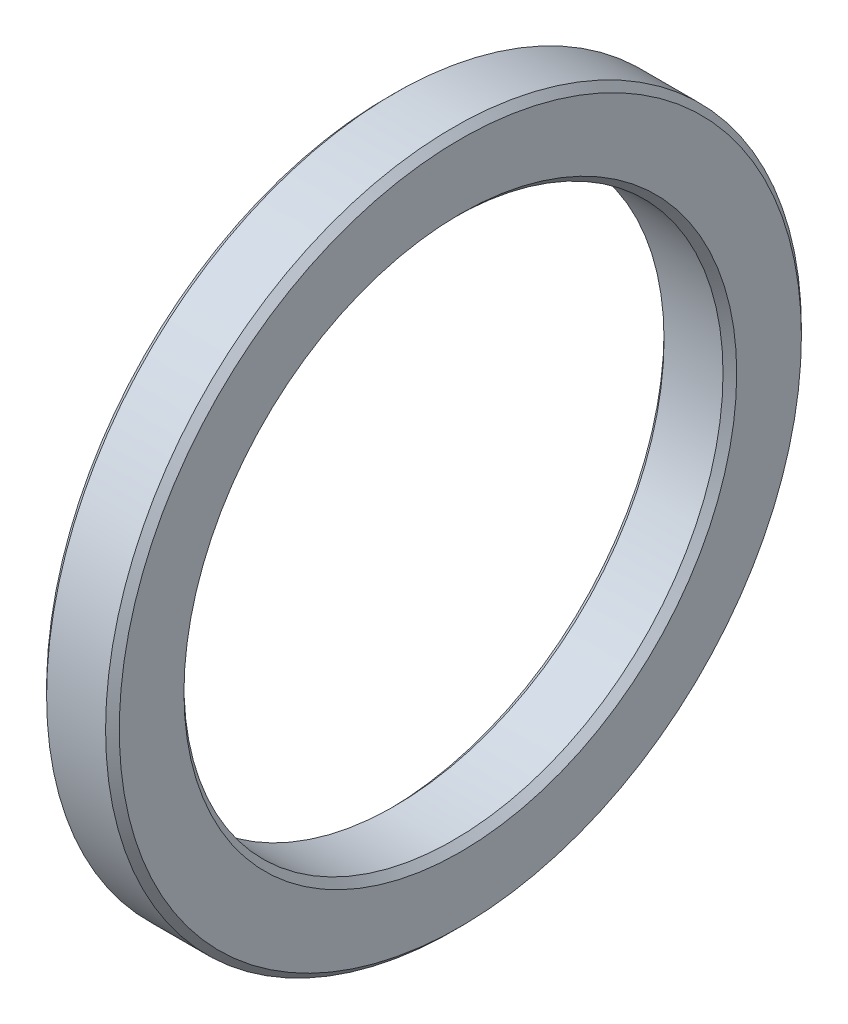
SolidWorks part; units mm, degrees
ref_plane "Front Plane" through (0, 0, 0) normal (0, 0, 1) x (1, 0, 0)
ref_plane "Top Plane" through (0, 0, 0) normal (0, 1, 0) x (1, 0, 0)
ref_plane "Right Plane" through (0, 0, 0) normal (1, 0, 0) x (0, 0, -1)
sketch "Sketch1" plane through (0, 0, 0) normal (1, 0, 0) x (0, 0, -1)
  circle A0 centre (0, 0) radius 32.27
  circle A1 centre (0, 0) radius 25
  dimension "D1" = 64.54
  dimension "D2" = 7.27
extrude "Boss-Extrude1" add sketch "Sketch1" along normal blind 6.74
chamfer "Chamfer1" distance 0.635 angle 45 2 edges at (0, 0, -32.27) (6.74, 0, -32.27)
chamfer "Chamfer2" distance 0.635 angle 45 2 edges at (0, 0, -25) (6.74, 0, -25)
